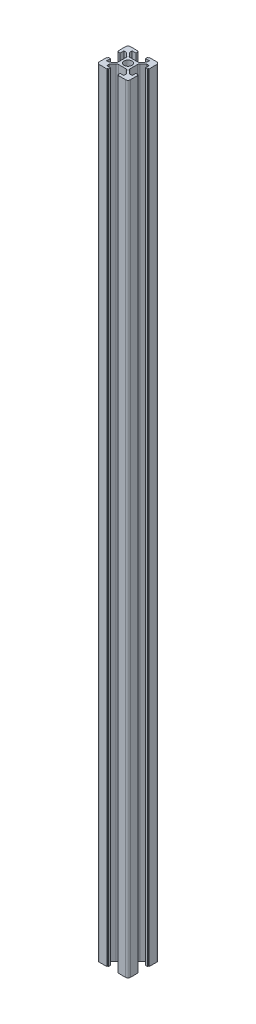
SolidWorks part; units mm, degrees
ref_plane "Front Plane" through (0, 0, 0) normal (0, 0, 1) x (1, 0, 0)
ref_plane "Top Plane" through (0, 0, 0) normal (0, 1, 0) x (1, 0, 0)
ref_plane "Right Plane" through (0, 0, 0) normal (1, 0, 0) x (0, 0, -1)
sketch "Sketch1" plane through (0, 0, 0) normal (0, 1, 0) x (1, 0, 0)
  line L0 (10, 0) -> (3.8, 0) construction
  line L1 (-8.5, -10) -> (8.5, -10)
  line L2 (-10, -8.5) -> (-10, 8.5)
  line L3 (-8.5, 10) -> (8.5, 10)
  line L4 (10, -8.5) -> (10, -3.6)
  line L5 (-10, -10) -> (10, 10) construction
  line L6 (-10, 10) -> (10, -10) construction
  line L7 (3.8, -2.4101) -> (3.8, 2.4101)
  line L8 (9.5, -3.1) -> (9.5, 3.1)
  line L9 (9.5, 3.1) -> (8.2, 3.1)
  line L10 (9.5, 3.1) -> (9.5, 3.6)
  line L11 (9.5, -3.1) -> (9.5, -3.6)
  line L12 (9.5, -3.6) -> (10, -3.6)
  line L13 (9.5, 3.6) -> (10, 3.6)
  line L14 (10, 3.6) -> (10, 8.5)
  line L15 (9.5, -3.1) -> (8.2, -3.1)
  line L16 (8.2, -3.1) -> (3.8, -3.1) construction
  line L17 (8.2, 3.1) -> (3.8, 3.1) construction
  line L18 (8.2, 3.1) -> (8.2, 5.5)
  line L19 (8.2, -3.1) -> (8.2, -5.5)
  line L20 (8.2, -5.5) -> (6.6, -5.5)
  line L21 (8.2, 5.5) -> (6.6, 5.5)
  line L22 (6.6, 5.5) -> (4.3238, 3.549)
  line L23 (6.6, -5.5) -> (4.3238, -3.549)
  line L24 (-5.5, -6.6) -> (-3.549, -4.3238)
  line L25 (-5.5, -8.2) -> (-5.5, -6.6)
  line L26 (-3.1, -8.2) -> (-5.5, -8.2)
  line L27 (-2.4101, -3.8) -> (2.4101, -3.8)
  line L28 (5.5, -6.6) -> (3.549, -4.3238)
  line L29 (5.5, -8.2) -> (5.5, -6.6)
  line L30 (3.1, -8.2) -> (5.5, -8.2)
  line L31 (3.1, -9.5) -> (3.1, -8.2)
  line L32 (3.1, -9.5) -> (3.6, -9.5)
  line L33 (3.6, -9.5) -> (3.6, -10)
  line L34 (-3.6, -9.5) -> (-3.6, -10)
  line L35 (-3.1, -9.5) -> (-3.6, -9.5)
  line L36 (-3.1, -9.5) -> (-3.1, -8.2)
  line L37 (-6.6, 5.5) -> (-4.3238, 3.549)
  line L38 (-8.2, 5.5) -> (-6.6, 5.5)
  line L39 (-8.2, 3.1) -> (-8.2, 5.5)
  line L40 (-3.8, 2.4101) -> (-3.8, -2.4101)
  line L41 (-6.6, -5.5) -> (-4.3238, -3.549)
  line L42 (-8.2, -5.5) -> (-6.6, -5.5)
  line L43 (-8.2, -3.1) -> (-8.2, -5.5)
  line L44 (-9.5, -3.1) -> (-8.2, -3.1)
  line L45 (-9.5, -3.1) -> (-9.5, -3.6)
  line L46 (-9.5, -3.6) -> (-10, -3.6)
  line L47 (-9.5, 3.6) -> (-10, 3.6)
  line L48 (-9.5, 3.1) -> (-9.5, 3.6)
  line L49 (-9.5, 3.1) -> (-8.2, 3.1)
  line L50 (5.5, 6.6) -> (3.549, 4.3238)
  line L51 (5.5, 8.2) -> (5.5, 6.6)
  line L52 (3.1, 8.2) -> (5.5, 8.2)
  line L53 (2.4101, 3.8) -> (-2.4101, 3.8)
  line L54 (-5.5, 6.6) -> (-3.549, 4.3238)
  line L55 (-5.5, 8.2) -> (-5.5, 6.6)
  line L56 (-3.1, 8.2) -> (-5.5, 8.2)
  line L57 (-3.1, 9.5) -> (-3.1, 8.2)
  line L58 (-3.1, 9.5) -> (-3.6, 9.5)
  line L59 (-3.6, 9.5) -> (-3.6, 10)
  line L60 (3.6, 9.5) -> (3.6, 10)
  line L61 (3.1, 9.5) -> (3.6, 9.5)
  line L62 (3.1, 9.5) -> (3.1, 8.2)
  circle A0 centre (0, 0) radius 2.5
  arc A1 (8.5, 10) -> (10, 8.5) centre (8.5, 8.5) cw
  arc A2 (8.5, -10) -> (10, -8.5) centre (8.5, -8.5) ccw
  arc A3 (-8.5, -10) -> (-10, -8.5) centre (-8.5, -8.5) cw
  arc A4 (-10, 8.5) -> (-8.5, 10) centre (-8.5, 8.5) cw
  arc A5 (3.8, -2.4101) -> (4.3238, -3.549) centre (5.3, -2.4101) ccw
  arc A6 (4.3238, 3.549) -> (3.8, 2.4101) centre (5.3, 2.4101) ccw
  arc A7 (-2.4101, -3.8) -> (-3.549, -4.3238) centre (-2.4101, -5.3) ccw
  arc A8 (3.549, -4.3238) -> (2.4101, -3.8) centre (2.4101, -5.3) ccw
  arc A9 (-3.8, 2.4101) -> (-4.3238, 3.549) centre (-5.3, 2.4101) ccw
  arc A10 (-4.3238, -3.549) -> (-3.8, -2.4101) centre (-5.3, -2.4101) ccw
  arc A11 (2.4101, 3.8) -> (3.549, 4.3238) centre (2.4101, 5.3) ccw
  arc A12 (-3.549, 4.3238) -> (-2.4101, 3.8) centre (-2.4101, 5.3) ccw
  point P0 (0, 0)
  point P25 (3.8, 0)
  point P28 (8.5, 0)
  dimension "D3" = 5
  dimension "D4" = 1.5
  dimension "D5" = 1.5
  dimension "D1" = 20
  dimension "D2" = 20
  dimension "D6" = 6.2
  dimension "D7" = 6.2
  dimension "D8" = 0.5
  dimension "D9" = 1.3
  dimension "D10" = 4
extrude "Boss-Extrude1" add sketch "Sketch1" along normal blind 500 contours A12 L54 L55 L56 L57 L58 L59 L3 A4 L2 L47 L48 L49 L39 L38 L37 A9 L40 A10 L41 L42 L43 L44 L45 L46 A3 L1 L34 L35 L36 L26 L25 L24 A7 L27 A8 L28 L29 L30 L31 L32 L33 A2 L4 L12 L11 L15 L19 L20
sketch "Sketch2" plane through (0, 0, -3.8) normal (0, 0, -1) x (-1, 0, 0)
  line L0 (0, 0) -> (0, 500) construction
  line L1 (-2.4101, 500) -> (2.4101, 500) construction
  circle A0 centre (0, 50) radius 3
  circle A1 centre (0, 130) radius 3
  circle A2 centre (0, 210) radius 3
  circle A3 centre (0, 290) radius 3
  circle A4 centre (0, 370) radius 3
  circle A5 centre (0, 450) radius 3
  point P2 (0, 0)
  point P8 (0, 0)
  point P19 (0, 0)
  point P20 (24.023, 162.7144)
  point P21 (48.3065, 212.74)
  point P22 (62.009, 250.0529)
  point P23 (0, 0)
  point P24 (0, 0)
  point P25 (0, 0)
  point P26 (0, 0)
  point P27 (0, 0)
  point P28 (0, 0)
  dimension "D1" = 50
  dimension "D2" = 80
  dimension "D3" = 80
  dimension "D4" = 80
  dimension "D5" = 80
  dimension "D6" = 80
extrude "Cut-Extrude1" cut sketch "Sketch2" against normal up to surface (7.6 mm away) up to face at (0, 250, 3.8)
